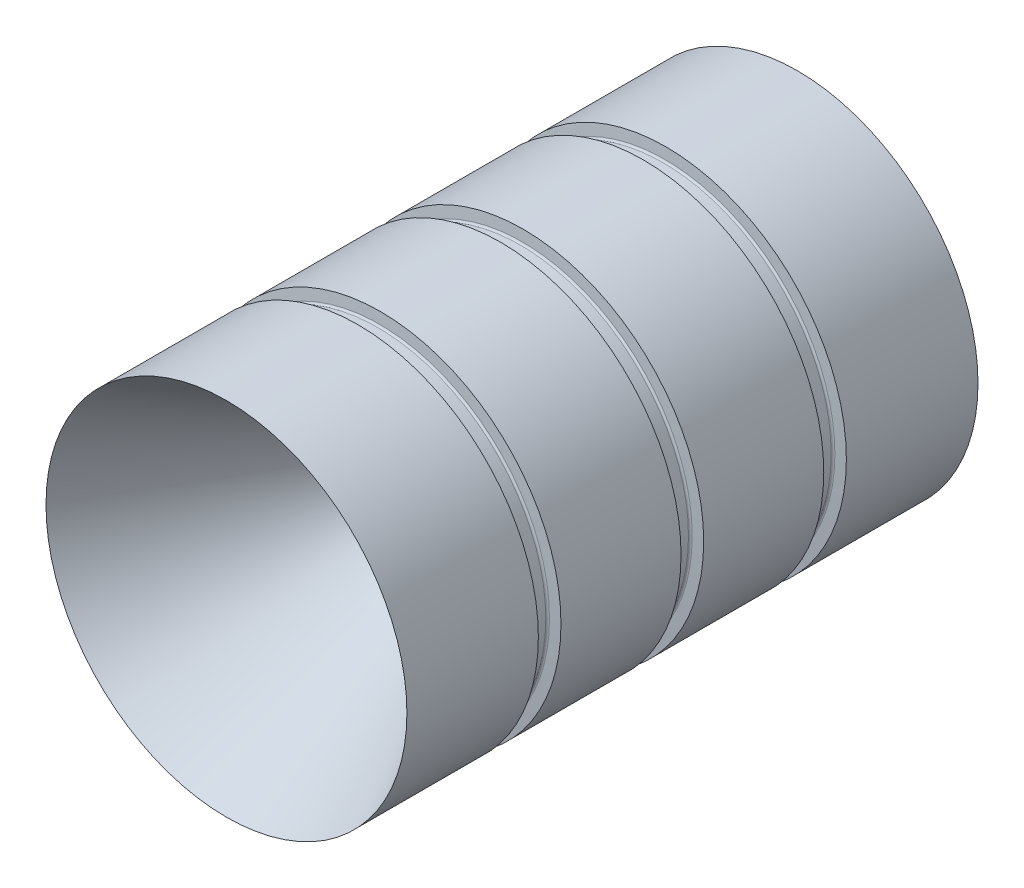
SolidWorks part; units mm, degrees
material "Cast Carbon Steel"
ref_plane "Front Plane" through (0, 0, 0) normal (0, 0, 1) x (1, 0, 0)
ref_plane "Top Plane" through (0, 0, 0) normal (0, 1, 0) x (1, 0, 0)
ref_plane "Right Plane" through (0, 0, 0) normal (1, 0, 0) x (0, 0, -1)
sketch "Sketch1" plane through (0, 0, 0) normal (1, 0, 0) x (0, 0, -1)
  line L1 (264.0086, 41.275) -> (309.0541, 15.268)
  line L2 (309.0541, 15.268) -> (315.1907, 15.268)
  line L3 (0, 0) -> (394.629, 0) construction
  line L4 (394.629, 41.275) -> (264.0086, 41.275)
  line L5 (309.0541, 15.268) -> (308.6626, 15.0461)
  line L6 (394.629, 41.275) -> (394.629, 34.5678)
  arc A0 (315.1907, 15.268) -> (317.157, 15.6094) centre (315.1907, 21.1003) ccw
  spline S0 degree 2 poles (317.157, 15.6094) (354.2503, 28.893) (394.629, 34.5678) knots 0 0 0 1 1 1
  dimension "D2" = 41.275
ref_plane "Plane1" through (0, 0, 0) normal (-1, 0, 0) x (0, -1, 0)
ref_plane "Plane2" through (0, 0, 0) normal (-1, 0, 0) x (0, -1, 0)
ref_plane "Plane3" through (0, 0, 0) normal (-1, 0, 0) x (0, -1, 0)
revolve "Revolve1" add sketch "Sketch1" angle 360 about L3
ref_plane "Plane4" through (0, 0, 0) normal (-1, 0, 0) x (0, -1, 0)
sketch "Sketch9" plane through (0, 0, 0) normal (-1, 0, 0) x (0, -1, 0)
  line L0 (38.8614, -294.2833) -> (41.3639, -294.0643)
  line L1 (41.3639, -294.0643) -> (41.3639, -299.252)
  line L2 (41.3639, -299.252) -> (38.8614, -299.0331)
  line L3 (38.4556, -298.5903) -> (38.4556, -294.7261)
  line L4 (0, 50) -> (0, -50) construction
  line L5 (-41.275, -394.629) -> (41.275, -394.629) construction
  arc A0 (38.8614, -299.0331) -> (38.4556, -298.5903) centre (38.9001, -298.5903) cw
  arc A1 (38.4556, -294.7261) -> (38.8614, -294.2833) centre (38.9001, -294.7261) cw
  dimension "D1" = 95.377
revolve "Groove for AS 568-234, O-Ring1" cut sketch "Sketch9"
ref_plane "Plane5" through (0, 0, 0) normal (-1, 0, 0) x (0, -1, 0)
sketch "Sketch11" plane through (0, 0, 0) normal (-1, 0, 0) x (0, -1, 0)
  line L0 (38.8614, -326.9223) -> (41.3639, -326.7033)
  line L1 (41.3639, -326.7033) -> (41.3639, -331.891)
  line L2 (41.3639, -331.891) -> (38.8614, -331.6721)
  line L3 (38.4556, -331.2293) -> (38.4556, -327.3651)
  line L4 (0, 50) -> (0, -50) construction
  line L5 (-41.275, -394.629) -> (41.275, -394.629) construction
  arc A0 (38.8614, -331.6721) -> (38.4556, -331.2293) centre (38.9001, -331.2293) cw
  arc A1 (38.4556, -327.3651) -> (38.8614, -326.9223) centre (38.9001, -327.3651) cw
  dimension "D1" = 62.738
revolve "Groove for AS 568-234, O-Ring2" cut sketch "Sketch11" angle 360 about L4
ref_plane "Plane6" through (0, 0, 0) normal (-1, 0, 0) x (0, -1, 0)
sketch "Sketch13" plane through (0, 0, 0) normal (-1, 0, 0) x (0, -1, 0)
  line L0 (38.8614, -359.5613) -> (41.3639, -359.3423)
  line L1 (41.3639, -359.3423) -> (41.3639, -364.53)
  line L2 (41.3639, -364.53) -> (38.8614, -364.3111)
  line L3 (38.4556, -363.8683) -> (38.4556, -360.0041)
  line L4 (0, 50) -> (0, -50) construction
  line L5 (-41.275, -394.629) -> (41.275, -394.629) construction
  arc A0 (38.8614, -364.3111) -> (38.4556, -363.8683) centre (38.9001, -363.8683) cw
  arc A1 (38.4556, -360.0041) -> (38.8614, -359.5613) centre (38.9001, -360.0041) cw
  dimension "D1" = 30.099
revolve "Groove for AS 568-234, O-Ring3" cut sketch "Sketch13" angle 360 about L4
